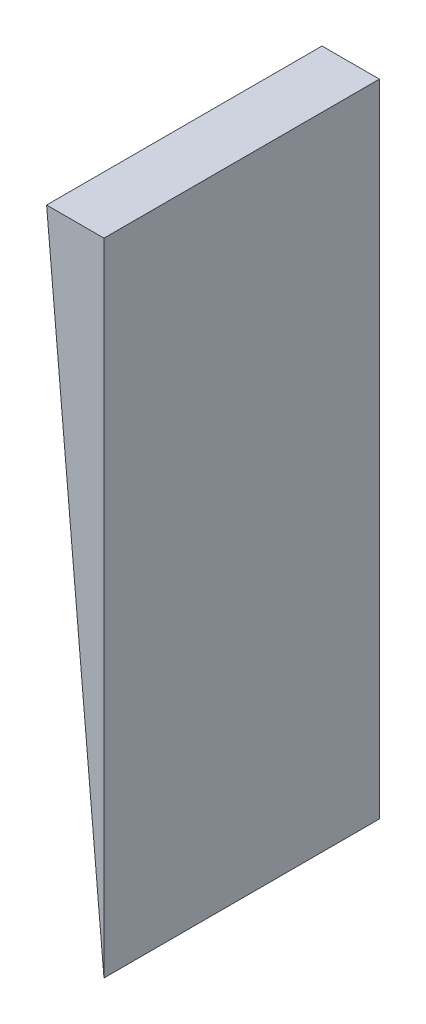
SolidWorks part; units mm, degrees
material "Rubber"
ref_plane "Front Plane" through (0, 0, 0) normal (0, 0, 1) x (1, 0, 0)
ref_plane "Top Plane" through (0, 0, 0) normal (0, 1, 0) x (1, 0, 0)
ref_plane "Right Plane" through (0, 0, 0) normal (1, 0, 0) x (0, 0, -1)
sketch "Sketch1" plane through (0, 0, 0) normal (0, 0, 1) x (1, 0, 0)
  line L0 (-15, 0) -> (0, -167.4979)
  line L1 (0, -167.4979) -> (0, 0)
  line L2 (0, 0) -> (-15, 0)
  point P3 (0, 0)
  point P4 (0, 0)
  dimension "D1" = 15
  dimension "D2" = 168.1682
extrude "Boss-Extrude1" add sketch "Sketch1" along normal blind 72
